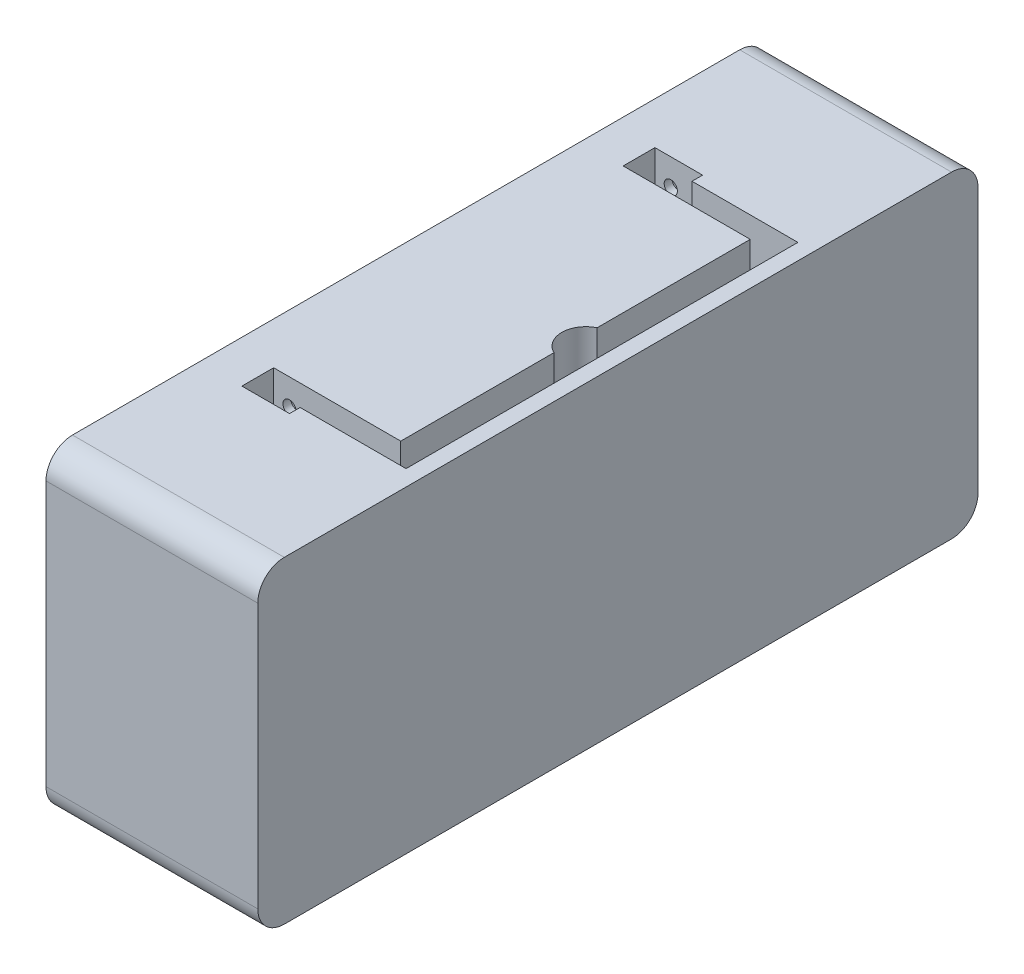
SolidWorks part; units mm, degrees
material "PBT General Purpose"
ref_plane "Front Plane" through (0, 0, 0) normal (0, 0, 1) x (1, 0, 0)
ref_plane "Top Plane" through (0, 0, 0) normal (0, 1, 0) x (1, 0, 0)
ref_plane "Right Plane" through (0, 0, 0) normal (1, 0, 0) x (0, 0, -1)
sketch "Sketch1" plane through (0, 0, 0) normal (1, 0, 0) x (0, 0, -1)
  line L1 (-63, -30) -> (63, -30)
  line L2 (-68, -25) -> (-68, 25)
  line L3 (-63, 30) -> (63, 30)
  line L4 (68, -25) -> (68, 25)
  line L5 (-68, -30) -> (68, 30) construction
  line L6 (-68, 30) -> (68, -30) construction
  arc A0 (63, 30) -> (68, 25) centre (63, 25) cw
  arc A1 (68, -25) -> (63, -30) centre (63, -25) cw
  arc A2 (-63, -30) -> (-68, -25) centre (-63, -25) cw
  arc A3 (-68, 25) -> (-63, 30) centre (-63, 25) cw
  point P0 (0, 0)
  dimension "D3" = 5
  dimension "D1" = 136
  dimension "D2" = 60
extrude "Boss-Extrude1" add sketch "Sketch1" against normal blind 40 contours L3 A0 L4 A1 L1 A2 L2 A3
sketch "Sketch3" plane through (0, 30, 0) normal (0, 1, 0) x (1, 0, 0)
  line L1 (-3.0096, -37) -> (-23.0096, -37)
  line L2 (-23.0096, -37) -> (-23.0096, -39)
  line L3 (-23.0096, -39) -> (-32.0096, -39)
  line L4 (-32.0096, -39) -> (-32.0096, -33)
  line L5 (-32.0096, -33) -> (-8.0096, -33)
  line L6 (-8.0096, -33) -> (-8.0096, -4.0673)
  line L7 (0, 0) -> (-42.4648, 0) construction
  line L8 (0, -63) -> (0, 63) construction
  line L15 (-3.0096, -37) -> (-3.0096, 37)
  line L16 (-8.0096, 33) -> (-8.0096, 4.0673)
  line L17 (-32.0096, 33) -> (-8.0096, 33)
  line L18 (-32.0096, 39) -> (-32.0096, 33)
  line L19 (-23.0096, 39) -> (-32.0096, 39)
  line L20 (-23.0096, 37) -> (-23.0096, 39)
  line L21 (-3.0096, 37) -> (-23.0096, 37)
  arc A1 (-8.0096, -4.0673) -> (-8.0096, 4.0673) centre (-6.0842, 0) cw
  point P15 (-3.0096, 0)
  point P16 (-3.0096, 0)
  point P17 (-8.0096, 0)
  dimension "D7" = 4.5
  dimension "D1" = 37
  dimension "D2" = 4
  dimension "D3" = 6
  dimension "D4" = 9
  dimension "D5" = 24
  dimension "D6" = 33
  dimension "D8" = 5
extrude "Cut-Extrude1" cut sketch "Sketch3" against normal blind 10
sketch "Sketch5" plane through (0, 0, -39) normal (0, 0, 1) x (1, 0, 0)
  line L0 (-40, 25) -> (0, 25) construction
  circle A0 centre (-29.0126, 25) radius 1.25
  dimension "D1" = 2.5
extrude "Cut-Extrude2" cut sketch "Sketch5" against normal blind 1.5 and the other way blind 7.5 contours A0
mirror "Mirror1" about plane through (0, 0, 0) normal (0, 0, 1) of "Cut-Extrude2"
